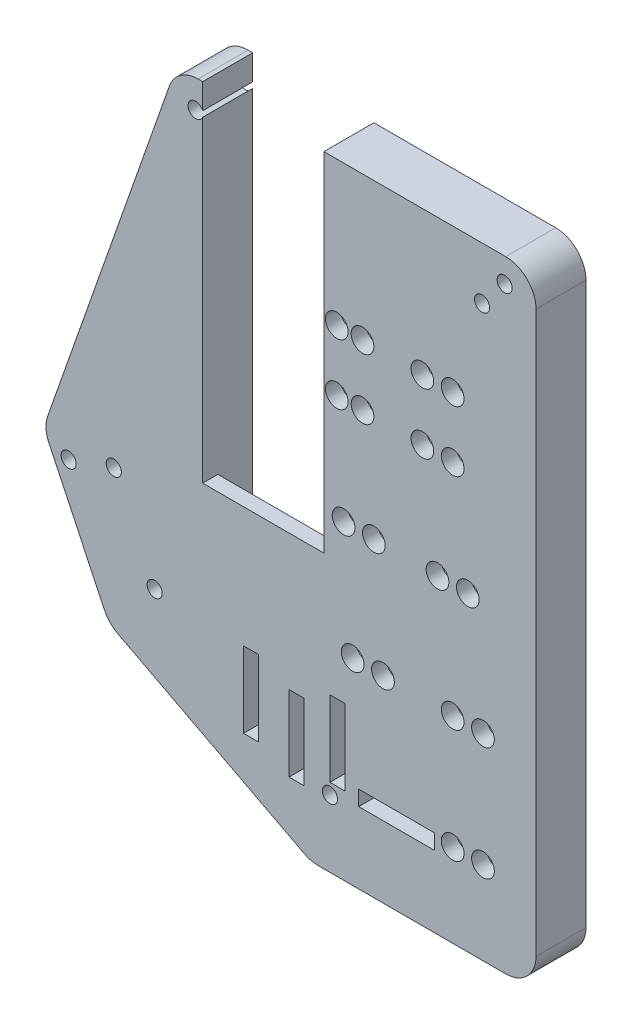
SolidWorks part; units mm, degrees
ref_plane "Front Plane" through (0, 0, 0) normal (0, 0, 1) x (1, 0, 0)
ref_plane "Top Plane" through (0, 0, 0) normal (0, 1, 0) x (1, 0, 0)
ref_plane "Right Plane" through (0, 0, 0) normal (1, 0, 0) x (0, 0, -1)
sketch "Sketch1" plane through (0, 0, 0) normal (0, 0, 1) x (1, 0, 0)
  line L6 (-20.066, -57.15) -> (46.99, -57.15) construction
  line L7 (-12.446, -73.152) -> (46.99, -73.152) construction
  line L8 (-3.3141, 6.35) -> (48.26, 6.35)
  line L9 (53.34, 1.27) -> (53.34, -92.71)
  line L10 (48.26, -97.79) -> (16.847, -97.79)
  line L16 (-8.1072, 2.9529) -> (-28.5162, -55.1739)
  line L18 (-20.066, -57.15) -> (-29.21, -57.15) construction
  line L26 (0, 0) -> (46.99, 0) construction
  line L27 (46.99, 0) -> (46.99, -88.9) construction
  line L28 (46.99, -88.9) -> (17.78, -88.9) construction
  line L29 (17.78, -88.9) -> (-12.446, -73.152) construction
  line L30 (-12.446, -73.152) -> (-20.066, -57.15) construction
  line L31 (-20.066, -57.15) -> (0, 0) construction
  line L32 (46.99, -57.15) -> (46.99, -88.9) construction
  line L33 (17.78, -88.9) -> (15.603, -97.79) construction
  line L34 (-12.446, -73.152) -> (-17.9301, -78.4424) construction
  line L35 (14.4997, -97.2152) -> (-16.7505, -80.9336)
  line L36 (-28.3096, -59.0409) -> (-18.9898, -78.6124)
  arc A0 (53.34, -92.71) -> (48.26, -97.79) centre (48.26, -92.71) cw
  arc A1 (14.4997, -97.2152) -> (16.847, -97.79) centre (16.847, -92.71) ccw
  arc A2 (-16.7505, -80.9336) -> (-18.9898, -78.6124) centre (-14.4033, -76.4284) cw
  arc A3 (-28.5162, -55.1739) -> (-28.3096, -59.0409) centre (-23.723, -56.8568) ccw
  arc A4 (-8.1072, 2.9529) -> (-3.3141, 6.35) centre (-3.3141, 1.27) cw
  arc A5 (48.26, 6.35) -> (53.34, 1.27) centre (48.26, 1.27) cw
  point P13 (53.34, -97.79)
  point P30 (53.34, 6.35)
  dimension "D8" = 5.08
  dimension "D1" = 88.9
  dimension "D2" = 29.21
  dimension "D3" = 59.436
  dimension "D4" = 67.056
  dimension "D5" = 104.14
  dimension "D6" = 82.55
  dimension "D7" = 46.99
  dimension "D13" = 103.76
  dimension "D17" = 108.51
extrude "Boss-Extrude1" add sketch "Sketch1" along normal blind 2.54
sketch "Sketch3" plane through (0, 0, 0) normal (0, 0, 1) x (1, 0, 0)
  line L8 (0, 0) -> (46.99, 0) construction
  line L9 (46.99, 0) -> (46.99, -88.9) construction
  line L10 (46.99, -88.9) -> (17.78, -88.9) construction
  line L11 (17.78, -88.9) -> (-12.446, -73.152) construction
  line L12 (-12.446, -73.152) -> (-20.066, -57.15) construction
  line L13 (-20.066, -57.15) -> (0, 0) construction
sketch "Sketch4" plane through (0, 0, 0) normal (0, 0, -1) x (-1, 0, 0)
  line L0 (-46.99, 0) -> (-46.99, -88.9) construction
  line L1 (0, 0) -> (-46.99, 0) construction
  line L2 (-46.99, -88.9) -> (-17.78, -88.9) construction
  line L8 (-17.78, -1.143) -> (2.54, -1.143)
  line L9 (-17.78, -1.143) -> (-17.78, -51.943)
  line L10 (-17.78, -51.943) -> (2.54, -51.943)
  line L11 (2.54, -1.143) -> (2.54, -51.943)
  circle A0 centre (-39.37, -17.78) radius 1.905
  circle A1 centre (-34.29, -17.78) radius 1.905
  circle A2 centre (-39.37, -27.94) radius 1.905
  circle A3 centre (-34.29, -27.94) radius 1.905
  circle A4 centre (-41.91, -45.72) radius 1.905
  circle A5 centre (-36.83, -45.72) radius 1.905
  circle A6 centre (-44.45, -64.77) radius 1.905
  circle A7 centre (-39.37, -64.77) radius 1.905
  circle A8 centre (-44.45, -83.82) radius 1.905
  circle A9 centre (-39.37, -83.82) radius 1.905
  circle A10 centre (-24.257, -17.78) radius 1.905
  circle A11 centre (-19.939, -17.78) radius 1.905
  circle A12 centre (-24.257, -27.94) radius 1.905
  circle A13 centre (-19.939, -27.94) radius 1.905
  circle A14 centre (-26.162, -45.72) radius 1.905
  circle A15 centre (-21.082, -45.72) radius 1.905
  circle A16 centre (-27.686, -64.77) radius 1.905
  circle A17 centre (-22.606, -64.77) radius 1.905
  dimension "D6" = 3.81
  dimension "D7" = 17.78
  dimension "D11" = 3.81
  dimension "D12" = 3.81
  dimension "D16" = 3.81
  dimension "D17" = 3.81
  dimension "D21" = 3.81
  dimension "D22" = 3.81
  dimension "D30" = 3.81
  dimension "D31" = 3.81
  dimension "D35" = 3.81
  dimension "D36" = 3.81
  dimension "D40" = 3.81
  dimension "D41" = 3.81
  dimension "D45" = 3.81
  dimension "D46" = 3.81
  dimension "D3" = 5.08
  dimension "D5" = 7.62
  dimension "D8" = 5.08
  dimension "D9" = 27.94
  dimension "D10" = 17.78
  dimension "D13" = 5.08
  dimension "D14" = 27.94
  dimension "D15" = 17.78
  dimension "D18" = 5.08
  dimension "D19" = 22.733
  dimension "D20" = 17.78
  dimension "D23" = 5.08
  dimension "D24" = 27.94
  dimension "D25" = 27.051
  dimension "D26" = 50.8
  dimension "D27" = 20.32
  dimension "D28" = 27.94
  dimension "D29" = 45.72
  dimension "D32" = 4.318
  dimension "D33" = 10.16
  dimension "D34" = 5.08
  dimension "D37" = 4.318
  dimension "D38" = 45.72
  dimension "D39" = 45.72
  dimension "D42" = 5.08
  dimension "D43" = 20.828
  dimension "D44" = 2.54
  dimension "D47" = 5.08
  dimension "D48" = 24.13
  dimension "D49" = 2.54
  dimension "D50" = 5.08
  dimension "D51" = 5.08
  dimension "D52" = 24.13
  dimension "D53" = 24.13
  dimension "D54" = 19.304
  dimension "D55" = 24.13
  dimension "D57" = 1.143
  dimension "D58" = 29.21
extrude "Cut-Extrude2" cut sketch "Sketch4" against normal blind 25.4
sketch "Sketch5" plane through (0, 0, 2.54) normal (0, 0, 1) x (1, 0, 0)
  line L0 (-2.54, -1.143) -> (-2.54, 6.35)
  line L1 (48.26, 6.35) -> (-3.3141, 6.35) construction
  line L2 (17.78, -1.143) -> (17.78, 6.35)
  line L3 (17.78, 6.35) -> (-2.54, 6.35)
  line L4 (-2.54, -1.143) -> (17.78, -1.143)
extrude "Cut-Extrude3" cut sketch "Sketch5" against normal blind 5.08
sketch "Sketch6" plane through (0, 0, 2.54) normal (0, 0, 1) x (1, 0, 0)
  line L0 (0, 0) -> (46.99, 0) construction
  line L1 (46.99, 0) -> (46.99, -88.9) construction
  line L2 (17.78, -88.9) -> (17.78, -82.3142) construction
  line L3 (46.99, -88.9) -> (17.78, -88.9) construction
  line L4 (17.78, -88.9) -> (-12.446, -73.152) construction
  line L5 (-12.446, -73.152) -> (-20.066, -57.15) construction
  circle A0 centre (1.6002, -2.4384) radius 1.27
  circle A1 centre (44.2976, -2.4384) radius 1.27
  circle A2 centre (-17.4498, -57.15) radius 1.27
  circle A4 centre (-10.5918, -71.3486) radius 1.27
  circle A5 centre (18.796, -86.5378) radius 1.27
  dimension "D1" = 2.54
  dimension "D3" = 2.54
  dimension "D7" = 2.54
  dimension "D9" = 2.54
  dimension "D11" = 2.54
  dimension "D2" = 2.4384
  dimension "D4" = 2.4384
  dimension "D5" = 2.6924
  dimension "D6" = 45.3898
  dimension "D8" = 2.6162
  dimension "D10" = 2.5866
  dimension "D12" = 1.016
  dimension "D13" = 2.3622
  dimension "D14" = 2.4561
  dimension "D15" = 2.3621
sketch "Sketch8" plane through (0, 0, 2.54) normal (0, 0, 1) x (1, 0, 0)
  line L0 (46.99, 0) -> (46.99, -88.9) construction
  line L1 (23.622, -83.2866) -> (36.322, -83.2866)
  line L2 (23.622, -83.2866) -> (23.622, -85.8266)
  line L3 (23.622, -85.8266) -> (36.322, -85.8266)
  line L4 (36.322, -83.2866) -> (36.322, -85.8266)
  line L5 (0, 0) -> (46.99, 0) construction
  line L7 (18.796, -72.009) -> (21.336, -72.009)
  line L8 (18.796, -72.009) -> (18.796, -84.709)
  line L9 (18.796, -84.709) -> (21.336, -84.709)
  line L10 (21.336, -72.009) -> (21.336, -84.709)
  line L11 (11.938, -74.676) -> (14.478, -74.676)
  line L12 (11.938, -74.676) -> (11.938, -87.376)
  line L13 (11.938, -87.376) -> (14.478, -87.376)
  line L14 (14.478, -74.676) -> (14.478, -87.376)
  line L15 (4.318, -72.136) -> (6.858, -72.136)
  line L16 (4.318, -72.136) -> (4.318, -84.836)
  line L17 (4.318, -84.836) -> (6.858, -84.836)
  line L18 (6.858, -72.136) -> (6.858, -84.836)
  dimension "D1" = 12.7
  dimension "D2" = 2.54
  dimension "D3" = 10.668
  dimension "D4" = 83.2866
  dimension "D5" = 12.7
  dimension "D6" = 2.54
  dimension "D7" = 25.654
  dimension "D8" = 72.009
  dimension "D9" = 12.7
  dimension "D10" = 2.54
  dimension "D11" = 32.512
  dimension "D12" = 74.676
  dimension "D13" = 12.7
  dimension "D14" = 2.54
  dimension "D15" = 72.136
  dimension "D16" = 40.132
extrude "Cut-Extrude5" cut sketch "Sketch8" against normal blind 5.08
sketch "Sketch9" plane through (0, 0, 0) normal (0, 0, -1) x (-1, 0, 0)
  line L0 (-48.26, -97.79) -> (-48.26, 1.27)
  line L1 (-48.26, 1.27) -> (-17.78, 1.27)
  line L2 (-17.78, 1.27) -> (-17.78, 6.35)
  line L3 (-17.78, 6.35) -> (-48.26, 6.35)
  line L4 (-53.34, -92.71) -> (-53.34, 1.27) construction
  line L5 (-53.34, 1.27) -> (-53.34, -92.71)
  line L6 (-17.78, 6.35) -> (-17.78, -51.943) construction
  line L7 (-48.26, 6.35) -> (-17.78, 6.35) construction
  line L9 (2.54, 0.8204) -> (2.54, -82.6092)
  line L12 (2.54, -51.943) -> (2.54, 6.35) construction
  line L13 (2.54, 0.8204) -> (2.54, 6.35)
  line L14 (3.3141, 6.35) -> (2.54, 6.35)
  line L15 (8.1072, 2.9529) -> (28.5162, -55.1739)
  line L17 (28.3096, -59.0409) -> (18.9898, -78.6124)
  line L18 (16.7505, -80.9336) -> (-14.4997, -97.2152)
  line L19 (-16.847, -97.79) -> (-16.847, -92.71)
  line L20 (-16.847, -92.71) -> (2.54, -82.6092)
  arc A0 (-53.34, -92.71) -> (-48.26, -97.79) centre (-48.26, -92.71) ccw
  arc A1 (-16.847, -97.79) -> (-14.4997, -97.2152) centre (-16.847, -92.71) ccw
  arc A2 (16.7505, -80.9336) -> (18.9898, -78.6124) centre (14.4033, -76.4284) ccw
  arc A3 (28.3096, -59.0409) -> (28.5162, -55.1739) centre (23.723, -56.8568) ccw
  arc A4 (3.3141, 6.35) -> (8.1072, 2.9529) centre (3.3141, 1.27) cw
  arc A5 (-48.26, 6.35) -> (-53.34, 1.27) centre (-48.26, 1.27) ccw
  dimension "D3" = 5.08
  dimension "D1" = 5.08
  dimension "D2" = 5.08
extrude "Boss-Extrude2" add sketch "Sketch9" along normal blind 5.842
sketch "Sketch10" plane through (0, 0, 2.54) normal (0, 0, 1) x (1, 0, 0)
  line L0 (48.26, 6.35) -> (17.78, 6.35) construction
  line L1 (53.34, -92.71) -> (53.34, 1.27) construction
  line L2 (-2.54, 6.35) -> (-3.3141, 6.35) construction
  line L3 (-8.1072, 2.9529) -> (-28.5162, -55.1739) construction
  line L4 (-28.3096, -59.0409) -> (-18.9898, -78.6124) construction
  circle A0 centre (48.0822, 2.286) radius 1.27
  circle A1 centre (-3.7187, 1.651) radius 1.27
  circle A2 centre (-25.0123, -59.762) radius 1.27
  dimension "D1" = 2.54
  dimension "D2" = 4.064
  dimension "D3" = 5.2578
  dimension "D4" = 4.699
  dimension "D5" = 4.572
  dimension "D6" = 2.667
  dimension "D7" = 4.826
extrude "Cut-Extrude6" cut sketch "Sketch10" against normal through all both and the other way through all
extrude "Cut-Extrude7" cut sketch "Sketch6" against normal through all both and the other way through all
